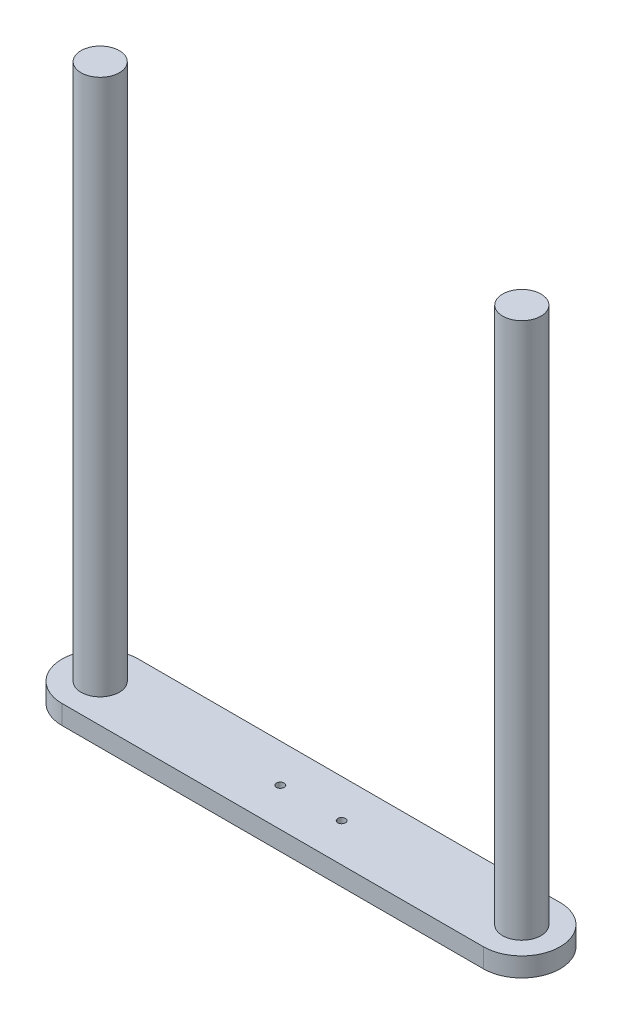
SolidWorks part; units mm, degrees
ref_plane "Front Plane" through (0, 0, 0) normal (0, 0, 1) x (1, 0, 0)
ref_plane "Top Plane" through (0, 0, 0) normal (0, 1, 0) x (1, 0, 0)
ref_plane "Right Plane" through (0, 0, 0) normal (1, 0, 0) x (0, 0, -1)
sketch "Sketch1" plane through (0, 0, 0) normal (0, 1, 0) x (1, 0, 0)
  line L1 (69.85, 12.7) -> (-69.85, 12.7)
  line L2 (69.85, 12.7) -> (69.85, -12.7)
  line L3 (69.85, -12.7) -> (-69.85, -12.7)
  line L4 (-69.85, 12.7) -> (-69.85, -12.7)
  line L5 (69.85, 12.7) -> (-69.85, -12.7) construction
  line L6 (69.85, -12.7) -> (-69.85, 12.7) construction
  arc A0 (-69.85, 12.7) -> (-69.85, -12.7) centre (-69.85, 0) ccw
  arc A1 (69.85, 12.7) -> (69.85, -12.7) centre (69.85, 0) cw
  point P0 (0, 0)
  dimension "D1" = 25.4
  dimension "D2" = 139.7
extrude "Boss-Extrude1" add sketch "Sketch1" along normal blind 6.35 contours L4 A0 | A1 L2 | L1 L4 L3 L2
sketch "Sketch2" plane through (0, 6.35, 0) normal (0, 1, 0) x (1, 0, 0)
  circle A0 centre (-69.85, 0) radius 6.35
  circle A1 centre (69.85, 0) radius 6.35
  point P4 (0, 0)
  point P7 (0, 0)
  point P8 (0, 0)
  dimension "D1" = 12.7
  dimension "D2" = 12.7
extrude "Boss-Extrude2" add sketch "Sketch2" along normal blind 177.8
sketch "Sketch3" plane through (0, 6.35, 0) normal (0, 1, 0) x (1, 0, 0)
  circle A0 centre (-10.16, 0) radius 1.27
  circle A1 centre (10.16, 0) radius 1.27
  point P4 (0, 0)
  point P6 (0, 0)
  point P7 (0, 0)
  dimension "D1" = 2.54
  dimension "D2" = 2.54
  dimension "D3" = 20.32
  dimension "D4" = 10.16
extrude "Cut-Extrude1" cut sketch "Sketch3" against normal through all
